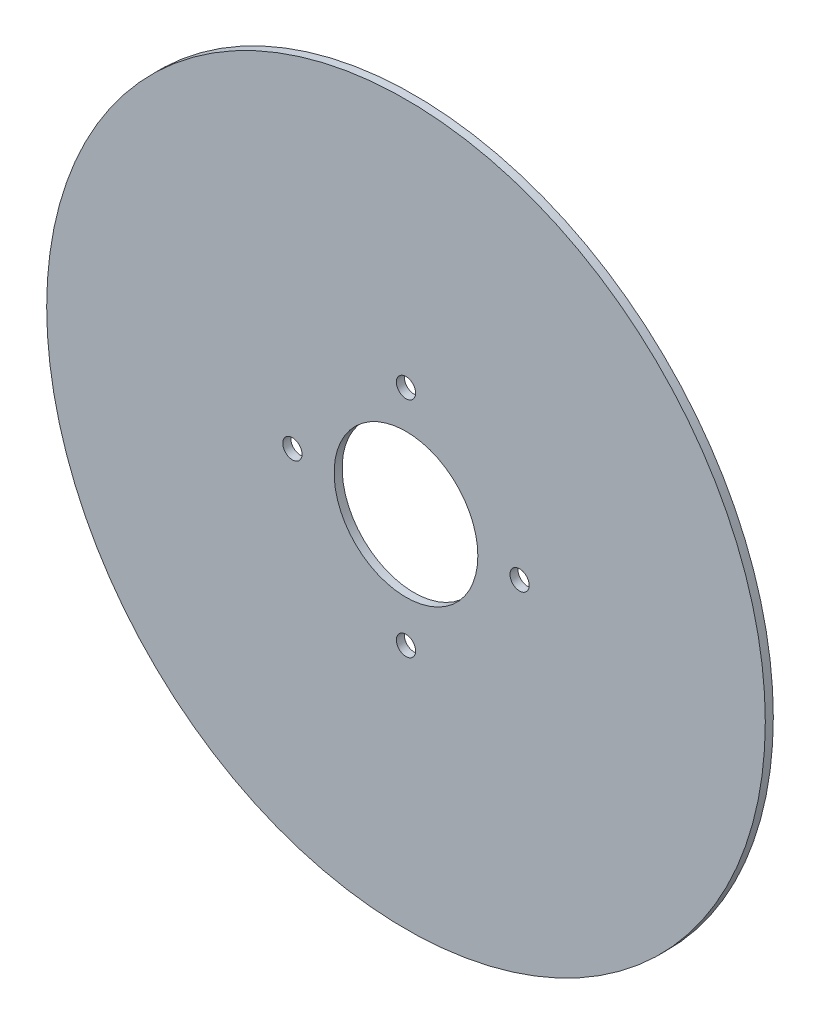
SolidWorks part; units mm, degrees
material "Hexcel AS4C (3000 Filaments)"
ref_plane "Front Plane" through (0, 0, 0) normal (0, 0, 1) x (1, 0, 0)
ref_plane "Top Plane" through (0, 0, 0) normal (0, 1, 0) x (1, 0, 0)
ref_plane "Right Plane" through (0, 0, 0) normal (1, 0, 0) x (0, 0, -1)
sketch "Sketch1" plane through (0, 0, 0) normal (0, 0, 1) x (1, 0, 0)
  circle A0 centre (0, 0) radius 11.2
  circle A1 centre (0, 0) radius 56
extrude "Extrude1" add sketch "Sketch1" along normal blind 1.25
sketch "Sketch2" plane through (0, 0, 1.25) normal (0, 0, 1) x (1, 0, 0)
  circle A0 centre (17.7, 0) radius 1.5
  circle A1 centre (0, -17.7) radius 1.5
  circle A2 centre (-17.7, 0) radius 1.5
  circle A3 centre (0, 17.1) radius 1.5
extrude "Extrude2" cut sketch "Sketch2" against normal up to surface (1.25 mm away) up to face at (56, 0, 0)
